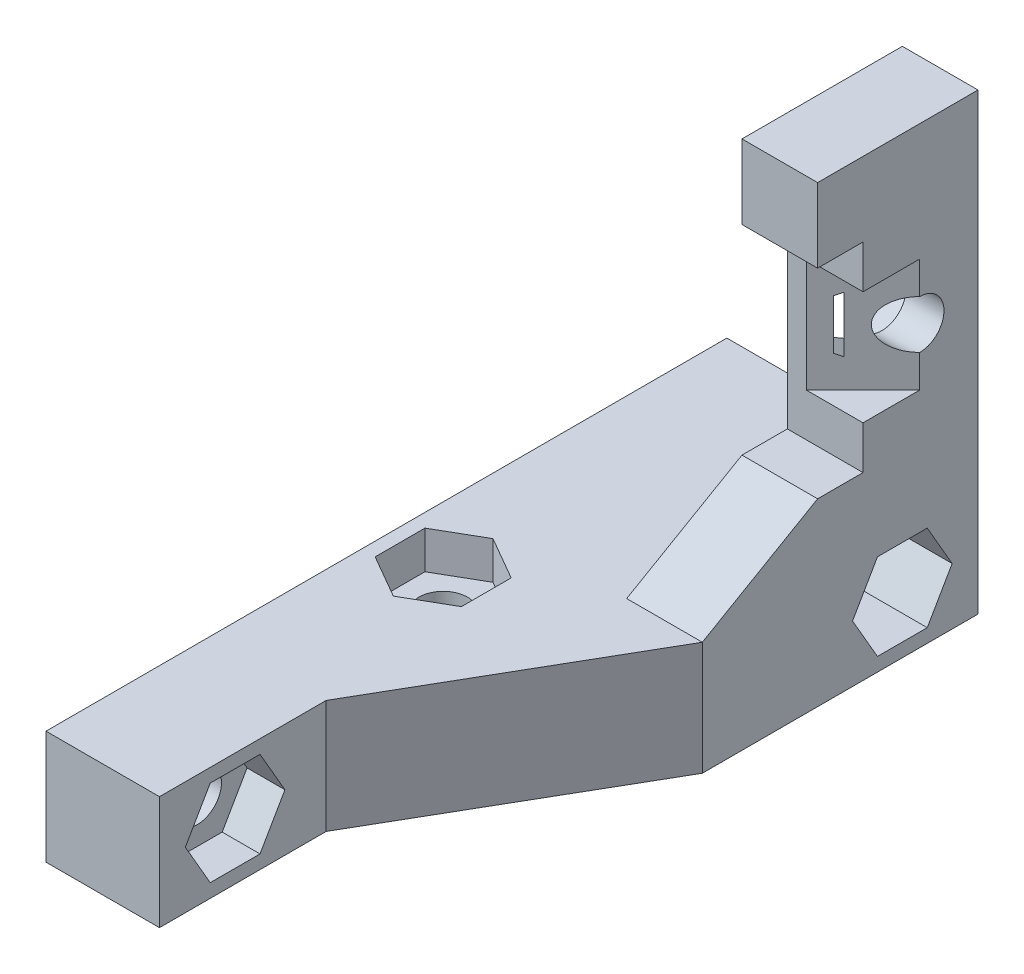
SolidWorks part; units mm, degrees
ref_plane "Alzado" through (0, 0, 0) normal (0, 0, 1) x (1, 0, 0)
ref_plane "Planta" through (0, 0, 0) normal (0, 1, 0) x (1, 0, 0)
ref_plane "Vista lateral" through (0, 0, 0) normal (1, 0, 0) x (0, 0, -1)
sketch "Croquis1" plane through (0, 0, 0) normal (0, 0, 1) x (1, 0, 0)
  line L0 (0, 0) -> (16.6, 0)
  line L1 (16.6, 0) -> (16.6, 30)
  line L2 (16.6, 30) -> (11.6, 30)
  line L3 (11.6, 30) -> (11.6, 7.5)
  line L4 (11.6, 7.5) -> (0, 7.5)
  line L5 (0, 7.5) -> (0, 0)
  dimension "D1" = 5
  dimension "D2" = 7.5
  dimension "D3" = 16.6
  dimension "D4" = 30
extrude "Saliente-Extruir1" add sketch "Croquis1" along normal blind 7.6
sketch "Croquis2" plane through (16.6, 0, 0) normal (1, 0, 0) x (0, 0, -1)
  line L0 (-3.85, 18.5) -> (-7.6, 18.5) construction
  line L1 (-7.6, 0) -> (-7.6, 30) construction
  circle A0 centre (-3.85, 18.5) radius 1.6
  dimension "D2" = 3.2
  dimension "D1" = 3.75
  dimension "D3" = 18.5
extrude "Cortar-Extruir1" cut sketch "Croquis2" against normal up to next
sketch "Croquis3" plane through (0, 0, 7.6) normal (0, 0, 1) x (1, 0, 0)
  line L0 (16.6, 0) -> (16.6, 30) construction
  line L1 (11.6, 30) -> (16.6, 30)
  line L2 (11.6, 30) -> (11.6, 25.1)
  line L3 (11.6, 25.1) -> (16.6, 25.1)
  line L4 (16.6, 30) -> (16.6, 25.1)
  line L5 (11.6, 11.9) -> (16.6, 11.9)
  line L6 (11.6, 30) -> (11.6, 7.5) construction
  line L7 (16.6, 11.9) -> (16.6, 0)
  line L8 (16.6, 0) -> (0, 0)
  line L9 (0, 0) -> (0, 7.5)
  line L10 (0, 7.5) -> (11.6, 7.5)
  line L11 (11.6, 7.5) -> (11.6, 11.9)
  line L12 (11.6, 20.1) -> (11.6, 16.9) construction
  line L13 (11.6, 20.1) -> (11.6, 16.9) construction
  line L14 (11.6, 18.5) -> (16.6, 18.5) construction
  line L15 (14.1, 18.5) -> (14.1, 25.1) construction
  line L16 (14.1, 18.5) -> (14.1, 11.9) construction
  point P21 (11.6, 18.5)
  dimension "D1" = 13.2
extrude "Saliente-Extruir2" add sketch "Croquis3" along normal blind 3
sketch "Croquis4" plane through (16.6, 0, 0) normal (1, 0, 0) x (0, 0, -1)
  line L1 (-10.6, 0) -> (-10.6, 11.9) construction
  line L2 (-10.6, 7.5) -> (-18.221, 7.5)
  line L3 (-18.221, 7.5) -> (-10.6, 11.9)
  line L4 (-10.6, 11.9) -> (-10.6, 7.5) construction
  line L5 (-10.6, 11.9) -> (-10.6, 7.5)
  dimension "D1" = 60
extrude "Saliente-Extruir3" add sketch "Croquis4" against normal up to surface (5 mm away) up to face at (11.6, 20.1, 3.85)
sketch "Croquis5" plane through (0, 0, 10.6) normal (0, 0, 1) x (1, 0, 0)
  line L10 (16.6, 0) -> (16.6, 7.5)
  line L11 (16.6, 7.5) -> (11.6, 7.5)
  line L12 (11.6, 7.5) -> (0, 7.5)
  line L13 (0, 7.5) -> (0, 0)
  line L14 (0, 0) -> (16.6, 0)
  line L15 (16.6, 0) -> (16.6, 7.5)
  line L16 (16.6, 7.5) -> (11.6, 7.5)
  line L17 (11.6, 7.5) -> (0, 7.5)
  line L18 (0, 7.5) -> (0, 0)
  line L19 (0, 0) -> (16.6, 0)
  dimension "D1" = 0
extrude "Saliente-Extruir4" add sketch "Croquis5" along normal up to vertex (7.621 mm away)
sketch "Croquis6" plane through (0, 0, 0) normal (0, -1, 0) x (1, 0, 0)
  line L0 (0, 18.221) -> (7.5, 18.221) construction
  line L1 (0, 18.221) -> (16.6, 18.221) construction
  line L2 (7.5, 18.221) -> (7.5, 33.9827)
  line L3 (7.5, 33.9827) -> (16.6, 18.221)
  line L4 (16.6, 18.221) -> (7.5, 18.221)
  dimension "D1" = 7.5
  dimension "D2" = 60
extrude "Saliente-Extruir5" add sketch "Croquis6" against normal up to surface (7.5 mm away) up to face at (5.8, 7.5, 9.1105)
ref_plane "Plano1" through (0, 0, 45) normal (0, 0, -1) x (-1, 0, 0)
sketch "Croquis7" plane through (0, 0, 18.221) normal (0, 0, 1) x (1, 0, 0)
  line L4 (7.5, 0) -> (7.5, 7.5)
  line L5 (7.5, 7.5) -> (0, 7.5)
  line L6 (0, 7.5) -> (0, 0)
  line L7 (0, 0) -> (7.5, 0)
  line L8 (7.5, 0) -> (7.5, 7.5)
  line L9 (7.5, 7.5) -> (0, 7.5)
  line L10 (0, 7.5) -> (0, 0)
  line L11 (0, 0) -> (7.5, 0)
  dimension "D1" = 0
extrude "Saliente-Extruir6" add sketch "Croquis7" along normal up to surface (26.779 mm away) up to plane "Plano1"
sketch "Croquis8" plane through (0, 0, 0) normal (-1, 0, 0) x (0, 0, 1)
  line L0 (5, 3.75) -> (40, 3.75) construction
  line L1 (0, 7.5) -> (0, 0) construction
  line L2 (45, 7.5) -> (45, 0) construction
  line L3 (40, 3.75) -> (45, 3.75) construction
  line L4 (5, 3.75) -> (0, 3.75) construction
  circle A0 centre (40, 3.75) radius 1.6
  circle A1 centre (5, 3.75) radius 1.6
  dimension "D1" = 3.2
  dimension "D2" = 35
extrude "Cortar-Extruir2" cut sketch "Croquis8" against normal up to next
sketch "Croquis9" plane through (11.6, 0, 0) normal (-1, 0, 0) x (0, 0, 1)
  line L1 (1, 16.8546) -> (3.85, 15.2091)
  line L2 (3.85, 15.2091) -> (6.7, 16.8546)
  line L3 (6.7, 16.8546) -> (6.7, 20.1454)
  line L4 (6.7, 20.1454) -> (3.85, 21.7909)
  line L5 (3.85, 21.7909) -> (1, 20.1454)
  line L6 (1, 20.1454) -> (1, 16.8546)
  circle A0 centre (3.85, 18.5) radius 2.85 construction
  dimension "D1" = 5.7
extrude "Cortar-Extruir3" cut sketch "Croquis9" against normal blind 2.5
sketch "Croquis10" plane through (7.5, 0, 0) normal (1, 0, 0) x (0, 0, -1)
  line L1 (-38.3546, 6.6) -> (-41.6454, 6.6)
  line L2 (-41.6454, 6.6) -> (-43.2909, 3.75)
  line L3 (-43.2909, 3.75) -> (-41.6454, 0.9)
  line L4 (-41.6454, 0.9) -> (-38.3546, 0.9)
  line L5 (-38.3546, 0.9) -> (-36.7091, 3.75)
  line L6 (-36.7091, 3.75) -> (-38.3546, 6.6)
  circle A0 centre (-40, 3.75) radius 2.85 construction
  dimension "D1" = 5.7
extrude "Cortar-Extruir4" cut sketch "Croquis10" against normal blind 2.5
sketch "Croquis11" plane through (16.6, 0, 0) normal (1, 0, 0) x (0, 0, -1)
  line L1 (-6.6454, 0.9) -> (-3.3546, 0.9)
  line L2 (-3.3546, 0.9) -> (-1.7091, 3.75)
  line L3 (-1.7091, 3.75) -> (-3.3546, 6.6)
  line L4 (-3.3546, 6.6) -> (-6.6454, 6.6)
  line L5 (-6.6454, 6.6) -> (-8.2909, 3.75)
  line L6 (-8.2909, 3.75) -> (-6.6454, 0.9)
  circle A0 centre (-5, 3.75) radius 2.85 construction
  dimension "D1" = 5.7
extrude "Cortar-Extruir5" cut sketch "Croquis11" against normal offset from surface (12.1 mm away) 4.5 up to face at (0, 2.15, 5)
sketch "Croquis12" plane through (0, 7.5, 0) normal (0, 1, 0) x (1, 0, 0)
  line L0 (3.75, -45) -> (3.75, 0) construction
  line L1 (7.5, -45) -> (0, -45) construction
  line L2 (11.6, 0) -> (0, 0) construction
  circle A0 centre (3.75, -22.5) radius 1.6
  dimension "D1" = 3.2
extrude "Cortar-Extruir6" cut sketch "Croquis12" against normal up to next
sketch "Croquis13" plane through (0, 7.5, 0) normal (0, -1, 0) x (1, 0, 0)
  line L1 (6.6, 20.8546) -> (6.6, 24.1454)
  line L2 (6.6, 24.1454) -> (3.75, 25.7909)
  line L3 (3.75, 25.7909) -> (0.9, 24.1454)
  line L4 (0.9, 24.1454) -> (0.9, 20.8546)
  line L5 (0.9, 20.8546) -> (3.75, 19.2091)
  line L6 (3.75, 19.2091) -> (6.6, 20.8546)
  circle A0 centre (3.75, 22.5) radius 2.85 construction
  dimension "D1" = 5.7
extrude "Cortar-Extruir7" cut sketch "Croquis13" along normal blind 2.5
ref_plane "Plano2" through (0, 18.5, 0) normal (0, 1, 0) x (-1, 0, 0)
sketch "Croquis14" plane through (0, 18.5, 0) normal (0, 1, 0) x (-1, 0, 0)
  line L1 (-16.6, 10.6) -> (-16.6, 7.6) construction
  line L2 (-16.6, 10.6) -> (-16.6, 7.6) construction
  line L3 (-16.6, 7.6) -> (-16.6, 3.85)
  line L4 (-16.6, 3.85) -> (-12.85, 7.6)
  line L5 (-12.85, 7.6) -> (-16.6, 7.6)
  dimension "D1" = 3.75
extrude "Cortar-Extruir8" cut sketch "Croquis14" against normal mid plane 7.5
